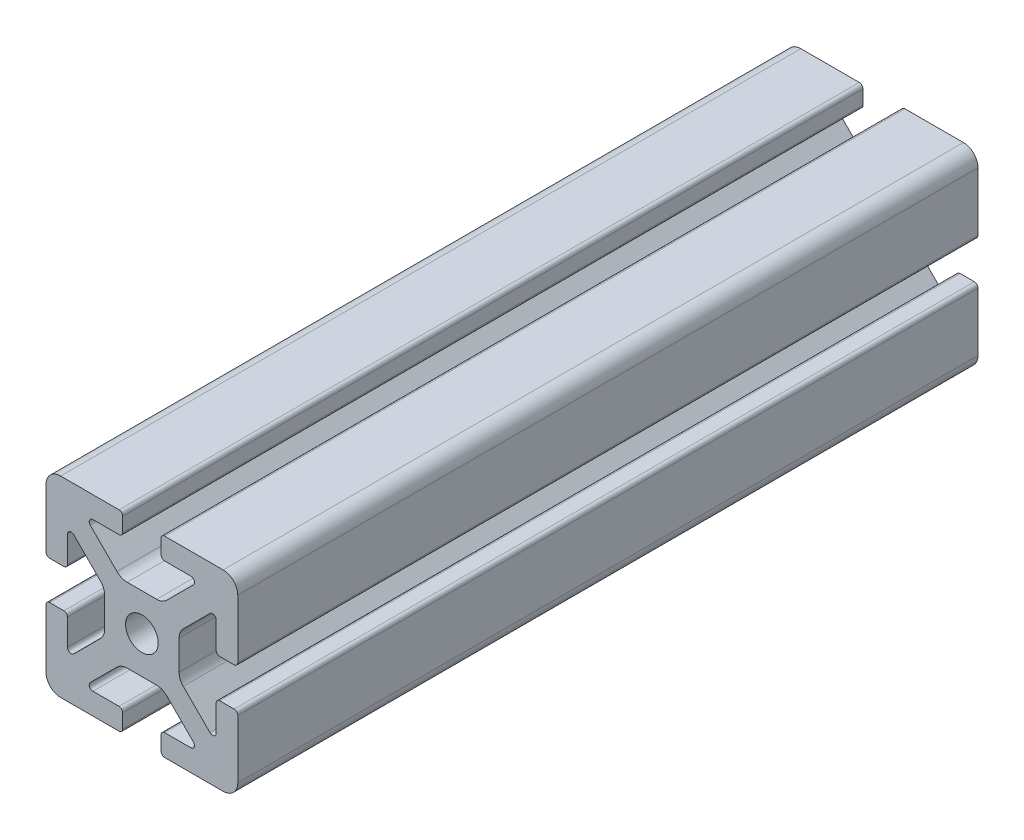
SolidWorks part; units mm, degrees
ref_plane "Front Plane" through (0, 0, 0) normal (0, 0, 1) x (1, 0, 0)
ref_plane "Top Plane" through (0, 0, 0) normal (0, 1, 0) x (1, 0, 0)
ref_plane "Right Plane" through (0, 0, 0) normal (1, 0, 0) x (0, 0, -1)
sketch "Sketch1" plane through (0, 0, 0) normal (0, 0, 1) x (1, 0, 0)
  line L2 (-20, 16.952) -> (-20, 4.7625)
  line L3 (-16.952, 20) -> (-4.7625, 20)
  line L4 (-4.0005, 19.238) -> (-4.0005, 16.2662)
  line L5 (-4.7625, 15.5042) -> (-10.2235, 15.5042)
  line L6 (-10.7623, 14.2034) -> (-5.194, 8.6351)
  line L7 (-14.2034, 10.7623) -> (-8.6351, 5.194)
  line L8 (-15.5042, 10.2235) -> (-15.5042, 4.7625)
  line L9 (-16.2662, 4.0005) -> (-19.238, 4.0005)
  line L11 (-3.0746, 7.7572) -> (3.0746, 7.7572)
  line L12 (-7.7572, 3.0746) -> (-7.7572, -3.0746)
  line L13 (16.2662, 4.0005) -> (19.238, 4.0005)
  line L14 (15.5042, 10.2235) -> (15.5042, 4.7625)
  line L15 (20, 16.952) -> (20, 4.7625)
  line L16 (16.952, 20) -> (4.7625, 20)
  line L17 (4.0005, 19.238) -> (4.0005, 16.2662)
  line L18 (4.7625, 15.5042) -> (10.2235, 15.5042)
  line L19 (7.7572, 3.0746) -> (7.7572, -3.0746)
  line L20 (10.7623, 14.2034) -> (5.194, 8.6351)
  line L21 (14.2034, 10.7623) -> (8.6351, 5.194)
  line L22 (-16.2662, -4.0005) -> (-19.238, -4.0005)
  line L23 (-15.5042, -10.2235) -> (-15.5042, -4.7625)
  line L24 (-14.2034, -10.7623) -> (-8.6351, -5.194)
  line L25 (-10.7623, -14.2034) -> (-5.194, -8.6351)
  line L26 (-4.7625, -15.5042) -> (-10.2235, -15.5042)
  line L27 (-4.0005, -19.238) -> (-4.0005, -16.2662)
  line L28 (-16.952, -20) -> (-4.7625, -20)
  line L29 (-20, -16.952) -> (-20, -4.7625)
  line L30 (20, -16.952) -> (20, -4.7625)
  line L31 (16.952, -20) -> (4.7625, -20)
  line L32 (4.0005, -19.238) -> (4.0005, -16.2662)
  line L33 (4.7625, -15.5042) -> (10.2235, -15.5042)
  line L34 (10.7623, -14.2034) -> (5.194, -8.6351)
  line L35 (14.2034, -10.7623) -> (8.6351, -5.194)
  line L36 (15.5042, -10.2235) -> (15.5042, -4.7625)
  line L37 (16.2662, -4.0005) -> (19.238, -4.0005)
  line L38 (-3.0746, -7.7572) -> (3.0746, -7.7572)
  circle A0 centre (0, 0) radius 3.4036
  arc A1 (-20, 16.952) -> (-16.952, 20) centre (-16.952, 16.952) cw
  arc A2 (-14.2034, 10.7623) -> (-15.5042, 10.2235) centre (-14.7422, 10.2235) ccw
  arc A3 (-10.2235, 15.5042) -> (-10.7623, 14.2034) centre (-10.2235, 14.7422) ccw
  arc A4 (-4.7625, 20) -> (-4.0005, 19.238) centre (-4.7625, 19.238) cw
  arc A5 (-20, 4.7625) -> (-19.238, 4.0005) centre (-19.238, 4.7625) ccw
  arc A6 (-15.5042, 4.7625) -> (-16.2662, 4.0005) centre (-16.2662, 4.7625) cw
  arc A7 (-4.0005, 16.2662) -> (-4.7625, 15.5042) centre (-4.7625, 16.2662) cw
  arc A8 (-3.0746, 7.7572) -> (-5.194, 8.6351) centre (-3.0746, 10.7544) cw
  arc A9 (-7.7572, 3.0746) -> (-8.6351, 5.194) centre (-10.7544, 3.0746) ccw
  arc A10 (15.5042, 4.7625) -> (16.2662, 4.0005) centre (16.2662, 4.7625) ccw
  arc A11 (20, 4.7625) -> (19.238, 4.0005) centre (19.238, 4.7625) cw
  arc A12 (20, 16.952) -> (16.952, 20) centre (16.952, 16.952) ccw
  arc A13 (4.7625, 20) -> (4.0005, 19.238) centre (4.7625, 19.238) ccw
  arc A14 (4.0005, 16.2662) -> (4.7625, 15.5042) centre (4.7625, 16.2662) ccw
  arc A15 (3.0746, 7.7572) -> (5.194, 8.6351) centre (3.0746, 10.7544) ccw
  arc A16 (7.7572, 3.0746) -> (8.6351, 5.194) centre (10.7544, 3.0746) cw
  arc A17 (14.2034, 10.7623) -> (15.5042, 10.2235) centre (14.7422, 10.2235) cw
  arc A18 (10.2235, 15.5042) -> (10.7623, 14.2034) centre (10.2235, 14.7422) cw
  arc A19 (-7.7572, -3.0746) -> (-8.6351, -5.194) centre (-10.7544, -3.0746) cw
  arc A20 (-3.0746, -7.7572) -> (-5.194, -8.6351) centre (-3.0746, -10.7544) ccw
  arc A21 (-4.0005, -16.2662) -> (-4.7625, -15.5042) centre (-4.7625, -16.2662) ccw
  arc A22 (-15.5042, -4.7625) -> (-16.2662, -4.0005) centre (-16.2662, -4.7625) ccw
  arc A23 (-20, -4.7625) -> (-19.238, -4.0005) centre (-19.238, -4.7625) cw
  arc A24 (-4.7625, -20) -> (-4.0005, -19.238) centre (-4.7625, -19.238) ccw
  arc A25 (-10.2235, -15.5042) -> (-10.7623, -14.2034) centre (-10.2235, -14.7422) cw
  arc A26 (-14.2034, -10.7623) -> (-15.5042, -10.2235) centre (-14.7422, -10.2235) cw
  arc A27 (-20, -16.952) -> (-16.952, -20) centre (-16.952, -16.952) ccw
  arc A28 (20, -16.952) -> (16.952, -20) centre (16.952, -16.952) cw
  arc A29 (14.2034, -10.7623) -> (15.5042, -10.2235) centre (14.7422, -10.2235) ccw
  arc A30 (10.2235, -15.5042) -> (10.7623, -14.2034) centre (10.2235, -14.7422) ccw
  arc A31 (4.7625, -20) -> (4.0005, -19.238) centre (4.7625, -19.238) cw
  arc A32 (20, -4.7625) -> (19.238, -4.0005) centre (19.238, -4.7625) ccw
  arc A33 (15.5042, -4.7625) -> (16.2662, -4.0005) centre (16.2662, -4.7625) cw
  arc A34 (4.0005, -16.2662) -> (4.7625, -15.5042) centre (4.7625, -16.2662) cw
  arc A35 (3.0746, -7.7572) -> (5.194, -8.6351) centre (3.0746, -10.7544) cw
  arc A36 (7.7572, -3.0746) -> (8.6351, -5.194) centre (10.7544, -3.0746) ccw
extrude "Boss-Extrude1" add sketch "Sketch1" along normal mid plane 760
sketch "Sketch2" plane through (0, 0, 0) normal (1, 0, 0) x (0, 0, -1)
  line L0 (-380, -20) -> (380, -20) construction
  line L1 (380, 20) -> (-225.6, 20)
  line L2 (380, 20) -> (380, -20)
  line L3 (380, -20) -> (-225.6, -20)
  line L4 (-225.6, 20) -> (-225.6, -20)
extrude "Cut-Extrude1" cut sketch "Sketch2" against normal blind 71 and the other way blind 65
